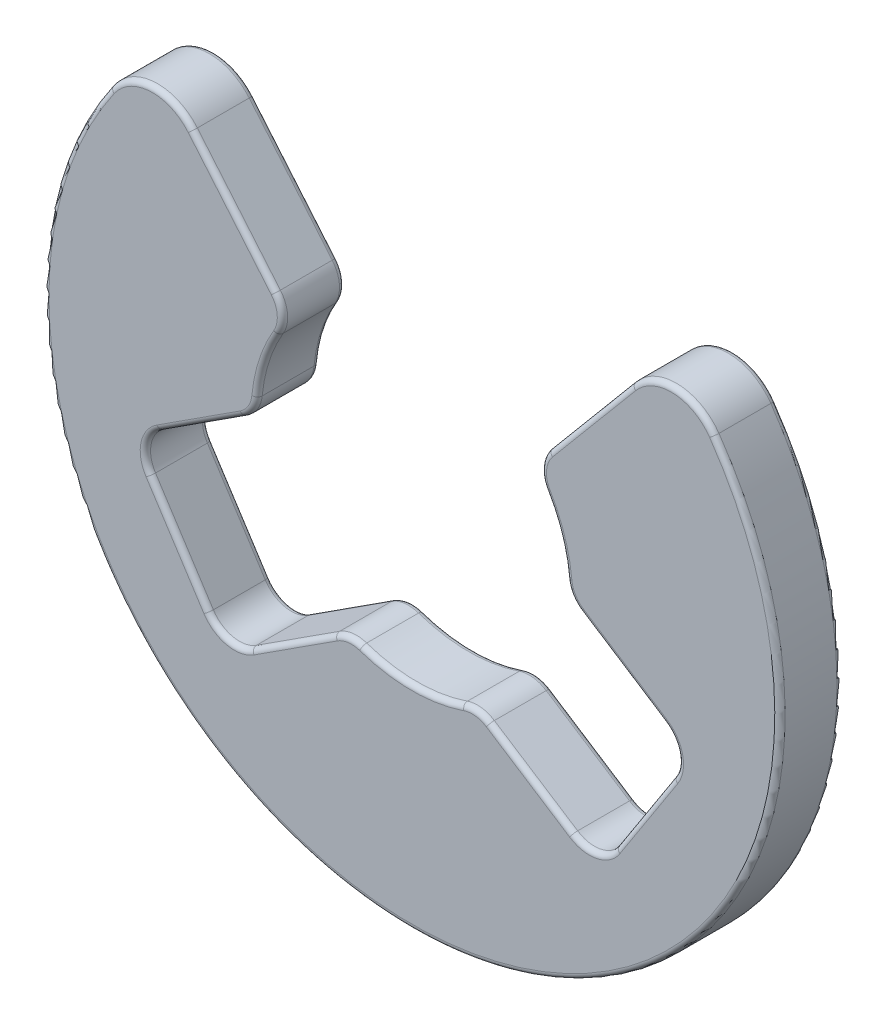
SolidWorks part; units mm, degrees
ref_plane "Front Plane" through (0, 0, 0) normal (0, 0, 1) x (1, 0, 0)
ref_plane "Top Plane" through (0, 0, 0) normal (0, 1, 0) x (1, 0, 0)
ref_plane "Right Plane" through (0, 0, 0) normal (1, 0, 0) x (0, 0, -1)
sketch "Sketch1" plane through (0, 0, 0) normal (0, 0, 1) x (1, 0, 0)
  line L0 (0, -1000) -> (0, 49000) construction
  line L1 (1.1713, 0.937) -> (2.5, 2.5204)
  line L2 (-1.1713, 0.937) -> (-2.5, 2.5204)
  line L3 (0.6164, -1.3675) -> (1.8012, -2.1331)
  line L4 (-1.5, 0) -> (-2.6848, -0.7656)
  line L5 (-0.6164, -1.3675) -> (-1.8012, -2.1331)
  line L6 (-2.6848, -0.7656) -> (-1.8012, -2.1331)
  line L7 (2.6848, -0.7656) -> (1.8012, -2.1331)
  line L8 (1.5, 0) -> (2.6848, -0.7656)
  arc A0 (-2.5, 2.5204) -> (2.5, 2.5204) centre (0, 0) ccw
  arc A1 (-1.1713, 0.937) -> (-1.5, 0) centre (0, 0) ccw
  arc A2 (-0.6164, -1.3675) -> (0.6164, -1.3675) centre (0, 0) ccw
  arc A3 (1.5, 0) -> (1.1713, 0.937) centre (0, 0) ccw
  dimension "D1" = 7.1
  dimension "D2" = 3
  dimension "D3" = 5
  dimension "D4" = 40
  dimension "D5" = 40
extrude "Boss-Extrude1" add sketch "Sketch1" along normal blind 0.6
fillet "Fillet1" radius 0.5 2 edges at (2.5, 2.5204, 0.3) (-2.5, 2.5204, 0.3)
fillet "Fillet2" radius 0.3 6 edges at (0.6164, -1.3675, 0.3) (-0.6164, -1.3675, 0.3) (1.5, 0, 0.3) (1.1713, 0.937, 0.3) (-1.5, 0, 0.3) (-1.1713, 0.937, 0.3)
fillet "Fillet3" radius 0.3 4 edges at (-1.8012, -2.1331, 0.3) (-2.6848, -0.7656, 0.3) (1.8012, -2.1331, 0.3) (2.6848, -0.7656, 0.3)
fillet "Fillet4" radius 0.05 48 edges at (-0.6194, -1.4052, 0) (-1.1475, -1.7106, 0) (-1.7751, -2.0116, 0) (-2.243, -1.4493, 0) (-2.5633, -0.7917, 0) (-2.0311, -0.3431, 0) (-1.5356, 0.0128, 0) (-1.4263, 0.4643, 0) (-1.2488, 0.9432, 0) (-1.7183, 1.5889, 0) (-2.524, 2.2441, 0) (0, -3.55, 0) (2.524, 2.2441, 0) (1.7183, 1.5889, 0) (1.2488, 0.9432, 0) (1.4263, 0.4643, 0) (1.5356, 0.0128, 0) (2.0311, -0.3431, 0) (2.5633, -0.7917, 0) (2.243, -1.4493, 0) (1.7751, -2.0116, 0) (1.1475, -1.7106, 0) (0.6194, -1.4052, 0) (0, -1.5, 0) (2.5633, -0.7917, 0.6) (2.0311, -0.3431, 0.6) (1.5356, 0.0128, 0.6) (1.4263, 0.4643, 0.6) (1.2488, 0.9432, 0.6) (1.7183, 1.5889, 0.6) (2.524, 2.2441, 0.6) (0, -3.55, 0.6) (-2.524, 2.2441, 0.6) (-1.7183, 1.5889, 0.6) (-1.2488, 0.9432, 0.6) (-1.4263, 0.4643, 0.6) (-1.5356, 0.0128, 0.6) (-2.0311, -0.3431, 0.6) (-2.5633, -0.7917, 0.6) (-2.243, -1.4493, 0.6) (-1.7751, -2.0116, 0.6) (-1.1475, -1.7106, 0.6) (-0.6194, -1.4052, 0.6) (0, -1.5, 0.6) (0.6194, -1.4052, 0.6) (1.1475, -1.7106, 0.6) (1.7751, -2.0116, 0.6) (2.243, -1.4493, 0.6)
